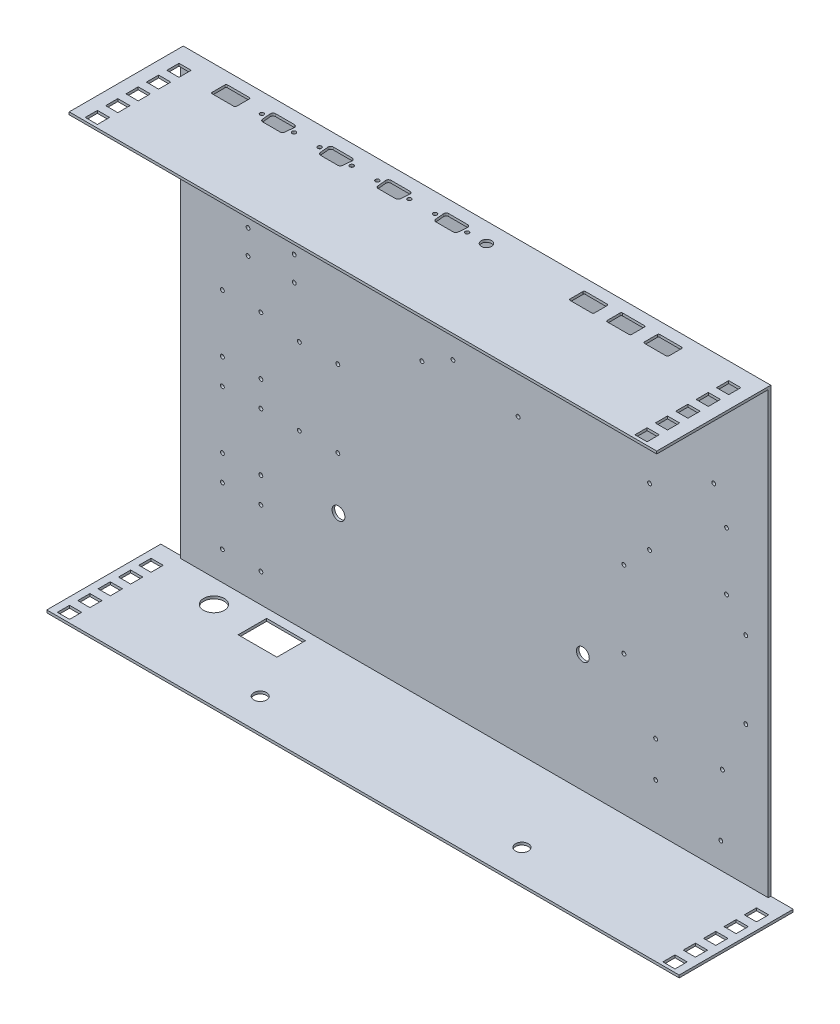
SolidWorks part; units mm, degrees
ref_plane "Front Plane" through (0, 0, 0) normal (0, 0, 1) x (1, 0, 0)
ref_plane "Top Plane" through (0, 0, 0) normal (0, 1, 0) x (1, 0, 0)
ref_plane "Right Plane" through (0, 0, 0) normal (1, 0, 0) x (0, 0, -1)
sketch "Sketch1" plane through (0, 0, 0) normal (0, 0, 1) x (1, 0, 0)
  line L13 (-229, -173.5) -> (229, -173.5)
  line L14 (-229, -173.5) -> (-229, 173.5)
  line L19 (-229, 173.5) -> (229, 173.5)
  line L20 (229, -173.5) -> (229, 173.5)
  line L21 (-229, -173.5) -> (229, 173.5) construction
  line L22 (-229, 173.5) -> (229, -173.5) construction
  point P0 (0, 0)
  dimension "D1" = 458
  dimension "D2" = 347
extrude "Boss-Extrude1" add sketch "Sketch1" along normal blind 2
sketch "Sketch4" plane through (0, -173.5, 0) normal (0, -1, 0) x (1, 0, 0)
  line L0 (-229, 2) -> (-229, 0) construction
  line L1 (-246.5, 0) -> (246.5, 0)
  line L2 (-246.5, 0) -> (-246.5, 88.9)
  line L3 (-246.5, 88.9) -> (246.5, 88.9)
  line L4 (246.5, 0) -> (246.5, 88.9)
  line L5 (229, 2) -> (229, 0) construction
  line L6 (-231.25, 88.9) -> (-231.25, 0) construction
  line L7 (-240.75, 61.02) -> (-231.25, 61.02)
  line L8 (-240.75, 86.4) -> (-231.25, 86.4)
  line L9 (-240.75, 86.4) -> (-240.75, 76.9)
  line L10 (-240.75, 76.9) -> (-231.25, 76.9)
  line L11 (-231.25, 86.4) -> (-231.25, 76.9)
  line L12 (-240.75, 70.52) -> (-240.75, 61.02)
  line L13 (-240.75, 70.52) -> (-231.25, 70.52)
  line L14 (-231.25, 70.52) -> (-231.25, 61.02)
  line L15 (-240.75, 45.14) -> (-231.25, 45.14)
  line L16 (-240.75, 54.64) -> (-240.75, 45.14)
  line L17 (-240.75, 54.64) -> (-231.25, 54.64)
  line L18 (-231.25, 54.64) -> (-231.25, 45.14)
  line L19 (-240.75, 29.26) -> (-231.25, 29.26)
  line L20 (-240.75, 38.76) -> (-240.75, 29.26)
  line L21 (-240.75, 38.76) -> (-231.25, 38.76)
  line L22 (-231.25, 38.76) -> (-231.25, 29.26)
  line L23 (-240.75, 13.38) -> (-231.25, 13.38)
  line L24 (-240.75, 22.88) -> (-240.75, 13.38)
  line L25 (-240.75, 22.88) -> (-231.25, 22.88)
  line L26 (-231.25, 22.88) -> (-231.25, 13.38)
  line L27 (0, 0) -> (0, 101.053) construction
  line L28 (231.25, 22.88) -> (231.25, 13.38)
  line L29 (240.75, 13.38) -> (231.25, 13.38)
  line L30 (240.75, 22.88) -> (240.75, 13.38)
  line L31 (240.75, 22.88) -> (231.25, 22.88)
  line L32 (231.25, 38.76) -> (231.25, 29.26)
  line L33 (240.75, 29.26) -> (231.25, 29.26)
  line L34 (240.75, 38.76) -> (240.75, 29.26)
  line L35 (240.75, 38.76) -> (231.25, 38.76)
  line L36 (240.75, 54.64) -> (240.75, 45.14)
  line L37 (231.25, 54.64) -> (231.25, 45.14)
  line L38 (240.75, 45.14) -> (231.25, 45.14)
  line L39 (240.75, 54.64) -> (231.25, 54.64)
  line L40 (231.25, 70.52) -> (231.25, 61.02)
  line L41 (240.75, 61.02) -> (231.25, 61.02)
  line L42 (240.75, 70.52) -> (231.25, 70.52)
  line L43 (240.75, 70.52) -> (240.75, 61.02)
  line L44 (231.25, 86.4) -> (231.25, 76.9)
  line L45 (240.75, 86.4) -> (231.25, 86.4)
  line L46 (240.75, 86.4) -> (240.75, 76.9)
  line L47 (240.75, 76.9) -> (231.25, 76.9)
  dimension "D1" = 17.5
  dimension "D2" = 17.5
  dimension "D3" = 88.9
  dimension "D4" = 2.25
  dimension "D5" = 9.5
  dimension "D6" = 2.5
  dimension "D7" = 9.5
  dimension "D9" = 15.88
  dimension "D8" = 5
extrude "Boss-Extrude4" add sketch "Sketch4" against normal blind 2
ref_plane "Plane1" through (0, 0, 0) normal (0, 1, 0) x (1, 0, 0)
mirror "Mirror1" about plane through (0, 0, 0) normal (0, 1, 0) of "Boss-Extrude4"
sketch "Sketch5" plane through (0, 173.5, 0) normal (0, 1, 0) x (1, 0, 0)
  line L0 (-229, 0) -> (-229, -88.9) construction
  line L1 (246.5, 0) -> (-246.5, 0) construction
  line L2 (246.5, -88.9) -> (-246.5, -88.9) construction
  line L3 (240.75, -76.9) -> (240.75, -86.4) construction
  line L4 (231.25, -86.4) -> (231.25, -76.9) construction
  line L5 (231.25, -76.9) -> (240.75, -76.9) construction
  line L6 (240.75, -70.52) -> (231.25, -70.52) construction
  line L7 (0, -1.1) -> (0, 1.1) construction
  line L8 (-231.25, -38.76) -> (-240.75, -38.76) construction
  line L9 (-231.25, -22.88) -> (-240.75, -22.88) construction
  line L11 (-229, 0) -> (-246.5, 0)
  line L12 (-229, 0) -> (-229, -88.9)
  line L13 (-229, -88.9) -> (-246.5, -88.9)
  line L14 (-246.5, 0) -> (-246.5, -88.9)
  line L15 (229, 0) -> (246.5, 0)
  line L16 (246.5, 0) -> (246.5, -88.9)
  line L17 (229, -88.9) -> (246.5, -88.9)
  line L18 (229, 0) -> (229, -88.9)
extrude "Cut-Extrude2" cut sketch "Sketch5" against normal up to next
sketch "Sketch6" plane through (0, 173.5, 0) normal (0, 1, 0) x (1, 0, 0)
  line L0 (-229, -88.9) -> (-229, 0) construction
  line L1 (-219, -13.32) -> (-209.5, -13.32)
  line L2 (-219, -13.32) -> (-219, -22.82)
  line L3 (-219, -22.82) -> (-209.5, -22.82)
  line L4 (-209.5, -13.32) -> (-209.5, -22.82)
  line L6 (-219, -29.22) -> (-219, -38.72)
  line L7 (-219, -29.22) -> (-209.5, -29.22)
  line L8 (-219, -38.72) -> (-209.5, -38.72)
  line L9 (-209.5, -29.22) -> (-209.5, -38.72)
  line L10 (-219, -45.12) -> (-219, -54.62)
  line L11 (-219, -45.12) -> (-209.5, -45.12)
  line L12 (-219, -54.62) -> (-209.5, -54.62)
  line L13 (-209.5, -45.12) -> (-209.5, -54.62)
  line L14 (-219, -61.02) -> (-219, -70.52)
  line L15 (-219, -61.02) -> (-209.5, -61.02)
  line L16 (-219, -70.52) -> (-209.5, -70.52)
  line L17 (-209.5, -61.02) -> (-209.5, -70.52)
  line L18 (-219, -76.92) -> (-219, -86.42)
  line L19 (-219, -76.92) -> (-209.5, -76.92)
  line L20 (-219, -86.42) -> (-209.5, -86.42)
  line L21 (-209.5, -76.92) -> (-209.5, -86.42)
  line L22 (0, -48.895) -> (0, 48.895) construction
  line L23 (219, -45.12) -> (209.5, -45.12)
  line L24 (219, -45.12) -> (219, -54.62)
  line L25 (209.5, -45.12) -> (209.5, -54.62)
  line L26 (219, -54.62) -> (209.5, -54.62)
  line L27 (219, -61.02) -> (209.5, -61.02)
  line L28 (209.5, -61.02) -> (209.5, -70.52)
  line L29 (219, -70.52) -> (209.5, -70.52)
  line L30 (219, -61.02) -> (219, -70.52)
  line L31 (219, -76.92) -> (219, -86.42)
  line L32 (219, -86.42) -> (209.5, -86.42)
  line L33 (209.5, -76.92) -> (209.5, -86.42)
  line L34 (219, -76.92) -> (209.5, -76.92)
  line L35 (219, -13.32) -> (219, -22.82)
  line L36 (219, -13.32) -> (209.5, -13.32)
  line L37 (209.5, -13.32) -> (209.5, -22.82)
  line L38 (219, -22.82) -> (209.5, -22.82)
  line L39 (219, -29.22) -> (219, -38.72)
  line L40 (219, -38.72) -> (209.5, -38.72)
  line L41 (209.5, -29.22) -> (209.5, -38.72)
  line L42 (219, -29.22) -> (209.5, -29.22)
  line L43 (229, -88.9) -> (-229, -88.9) construction
  dimension "D1" = 9.5
  dimension "D2" = 9.5
  dimension "D3" = 10
  dimension "D4" = 2.48
  dimension "D6" = 6.4
  dimension "D5" = 5
extrude "Cut-Extrude3" cut sketch "Sketch6" against normal up to next
sketch "Sketch9" plane through (0, 0, 2) normal (0, 0, 1) x (1, 0, 0)
  line L0 (-91, -171.5) -> (-91, 10.5) construction
  line L1 (246.5, -171.5) -> (-246.5, -171.5) construction
  line L2 (77, -171.5) -> (77, 10.5) construction
  line L3 (-229, -171.5) -> (229, -171.5) construction
  line L4 (-91, 10.5) -> (77, 10.5) construction
  line L5 (-229, 171.5) -> (-229, -171.5) construction
  circle A0 centre (-106, -79.5) radius 5
  circle A3 centre (84.5, -79.5) radius 5
  dimension "D5" = 10
  dimension "D6" = 10
  dimension "D1" = 138
  dimension "D2" = 168
  dimension "D3" = 182
  dimension "D8" = 15
  dimension "D9" = 90
  dimension "D14" = 15
  dimension "D15" = 90
extrude "Cut-Extrude4" cut sketch "Sketch9" against normal up to next
sketch "Sketch11" plane through (0, -173.5, 0) normal (0, -1, 0) x (1, 0, 0)
  line L0 (-90, 0) -> (-90, 85.1375) construction
  line L1 (-246.5, 0) -> (246.5, 0) construction
  line L2 (84, 0) -> (84, 87.0276) construction
  line L10 (-246.5, 88.9) -> (-246.5, 0) construction
  line L11 (-90, 79) -> (84, 79) construction
  circle A0 centre (-105, 64) radius 5
  circle A1 centre (99, 64) radius 5
  dimension "D4" = 10
  dimension "D5" = 10
  dimension "D1" = 174
  dimension "D2" = 156.5
  dimension "D3" = 79
  dimension "D6" = 15
  dimension "D7" = 15
  dimension "D8" = 15
  dimension "D9" = 15
extrude "Cut-Extrude5" cut sketch "Sketch11" against normal up to next
sketch "Sketch12" plane through (0, 0, 2) normal (0, 0, 1) x (1, 0, 0)
  line L0 (-229, -171.5) -> (229, -171.5) construction
  line L1 (-199, -151.5) -> (-164, -151.5)
  line L2 (-199, -151.5) -> (-199, -101.5)
  line L3 (-199, -101.5) -> (-164, -101.5)
  line L4 (-164, -151.5) -> (-164, -101.5)
  line L5 (-199, -151.5) -> (-164, -101.5) construction
  line L6 (-199, -101.5) -> (-164, -151.5) construction
  line L7 (-229, 171.5) -> (-229, -171.5) construction
  line L12 (-199, -86.5) -> (-164, -86.5)
  line L13 (-199, -86.5) -> (-199, -36.5)
  line L18 (-199, -36.5) -> (-164, -36.5)
  line L19 (-164, -86.5) -> (-164, -36.5)
  line L20 (-199, -101.5) -> (-199, 47.085) construction
  line L21 (-199, -86.5) -> (-164, -36.5) construction
  line L22 (-199, -36.5) -> (-164, -86.5) construction
  line L23 (-199, -21.5) -> (-164, -21.5)
  line L24 (-199, -21.5) -> (-199, 28.5)
  line L25 (-199, 28.5) -> (-164, 28.5)
  line L26 (-164, -21.5) -> (-164, 28.5)
  line L27 (-199, -21.5) -> (-164, 28.5) construction
  line L28 (-199, 28.5) -> (-164, -21.5) construction
  line L30 (-139, 23.5) -> (-104, 23.5)
  line L31 (-139, 23.5) -> (-139, -41.5)
  line L32 (-139, -41.5) -> (-104, -41.5)
  line L33 (-104, 23.5) -> (-104, -41.5)
  line L34 (-121.5, -41.5) -> (-121.5, 23.5) construction
  line L35 (-139, -9) -> (-104, -9) construction
  circle A0 centre (-196.5, -149) radius 1.5
  circle A1 centre (-166.5, -149) radius 1.5
  circle A2 centre (-166.5, -104) radius 1.5
  circle A3 centre (-196.5, -104) radius 1.5
  circle A12 centre (-196.5, -84) radius 1.5
  circle A13 centre (-166.5, -84) radius 1.5
  circle A14 centre (-166.5, -39) radius 1.5
  circle A15 centre (-196.5, -39) radius 1.5
  circle A16 centre (-196.5, -19) radius 1.5
  circle A17 centre (-166.5, -19) radius 1.5
  circle A18 centre (-166.5, 26) radius 1.5
  circle A19 centre (-196.5, 26) radius 1.5
  circle A20 centre (-136.5, 21) radius 1.5
  circle A21 centre (-106.5, 21) radius 1.5
  circle A22 centre (-106.5, -39) radius 1.5
  circle A23 centre (-136.5, -39) radius 1.5
  point P4 (-181.5, -126.5)
  point P21 (-181.5, -61.5)
  point P34 (-181.5, 3.5)
  point P43 (-181.5, 28.5)
  point P205 (-121.5, -9)
  dimension "D7" = 3
  dimension "D8" = 3
  dimension "D13" = 3
  dimension "D16" = 3
  dimension "D19" = 2.5
  dimension "D22" = 3
  dimension "D20" = 3
  dimension "D27" = 3
  dimension "D30" = 3
  dimension "D34" = 3
  dimension "D36" = 3
  dimension "D41" = 3
  dimension "D44" = 3
  dimension "D51" = 3
  dimension "D52" = 3
  dimension "D53" = 3
  dimension "D54" = 3
  dimension "D1" = 20
  dimension "D2" = 30
  dimension "D3" = 35
  dimension "D4" = 50
  dimension "D5" = 2.5
  dimension "D6" = 2.5
  dimension "D9" = 2.5
  dimension "D10" = 2.5
  dimension "D11" = 2.5
  dimension "D12" = 2.5
  dimension "D14" = 2.5
  dimension "D15" = 2.5
  dimension "D17" = 35
  dimension "D18" = 50
  dimension "D21" = 2.5
  dimension "D23" = 2.5
  dimension "D24" = 2.5
  dimension "D25" = 2.5
  dimension "D26" = 2.5
  dimension "D28" = 2.5
  dimension "D29" = 2.5
  dimension "D31" = 35
  dimension "D32" = 50
  dimension "D33" = 2.5
  dimension "D35" = 2.5
  dimension "D37" = 2.5
  dimension "D38" = 2.5
  dimension "D39" = 2.5
  dimension "D40" = 2.5
  dimension "D42" = 2.5
  dimension "D43" = 2.5
  dimension "D45" = 15
  dimension "D46" = 15
  dimension "D47" = 35
  dimension "D48" = 65
  dimension "D49" = 25
  dimension "D50" = 5
  dimension "D55" = 2.5
  dimension "D56" = 2.5
  dimension "D57" = 2.5
  dimension "D58" = 2.5
  dimension "D59" = 2.5
  dimension "D60" = 2.5
  dimension "D61" = 2.5
  dimension "D62" = 2.5
extrude "Cut-Extrude6" cut sketch "Sketch12" against normal blind 30 contours A0 | A1 | A12 | A13 | A15 | A14 | A16 | A3 | A2 | A17 | A23 | A22 | A20 | A21 | A18 | A19
sketch "Sketch15" plane through (0, 0, 2) normal (0, 0, 1) x (1, 0, 0)
  line L0 (35.28, 104.261) -> (-47.198, 104.261) construction
  line L1 (-179, 56.5) -> (-138, 56.5)
  line L2 (-179, 56.5) -> (-179, 80.5)
  line L3 (-179, 80.5) -> (-138, 80.5)
  line L4 (-138, 56.5) -> (-138, 80.5)
  line L5 (-158.5, 80.5) -> (-158.5, 56.5) construction
  line L6 (-179, 68.5) -> (-138, 68.5) construction
  line L7 (-64, 116.5) -> (56, 116.5)
  line L8 (-64, 116.5) -> (-64, 43.5)
  line L9 (-64, 43.5) -> (56, 43.5)
  line L10 (56, 116.5) -> (56, 43.5)
  line L11 (-4, 43.5) -> (-4, 116.5) construction
  line L12 (-64, 80) -> (56, 80) construction
  line L13 (94, 136.5) -> (189, 136.5)
  line L14 (94, 136.5) -> (94, 84.5)
  line L15 (94, 84.5) -> (189, 84.5)
  line L16 (189, 136.5) -> (189, 84.5)
  line L17 (141.5, 84.5) -> (141.5, 136.5) construction
  line L18 (94, 110.5) -> (189, 110.5) construction
  line L19 (134, 64.5) -> (199, 64.5)
  line L20 (134, 64.5) -> (134, 14.5)
  line L21 (134, 14.5) -> (199, 14.5)
  line L22 (199, 64.5) -> (199, 14.5)
  line L23 (166.5, 14.5) -> (166.5, 64.5) construction
  line L24 (134, 39.5) -> (199, 39.5) construction
  line L25 (114, -0.5) -> (214, -0.5)
  line L26 (114, -0.5) -> (114, -65.5)
  line L27 (114, -65.5) -> (214, -65.5)
  line L28 (214, -0.5) -> (214, -65.5)
  line L29 (164, -65.5) -> (164, -0.5) construction
  line L30 (114, -33) -> (214, -33) construction
  line L31 (138.725, -90.5) -> (214, -90.5)
  line L32 (138.725, -90.5) -> (138.725, -163.5)
  line L33 (138.725, -163.5) -> (214, -163.5)
  line L34 (214, -90.5) -> (214, -163.5)
  line L35 (176.3625, -163.5) -> (176.3625, -90.5) construction
  line L36 (138.725, -127) -> (214, -127) construction
  line L41 (-229, 171.5) -> (-229, -171.5) construction
  line L42 (229, 171.5) -> (-229, 171.5) construction
  line L43 (229, -171.5) -> (229, 171.5) construction
  line L44 (96.5, 87) -> (186.5, 87)
  line L45 (-176.5, 59) -> (-140.5, 59)
  line L46 (-176.5, 59) -> (-176.5, 78)
  line L47 (-176.5, 78) -> (-140.5, 78)
  line L48 (-140.5, 59) -> (-140.5, 78)
  line L49 (-176.5, 59) -> (-140.5, 78) construction
  line L50 (-176.5, 78) -> (-140.5, 59) construction
  line L51 (96.5, 87) -> (96.5, 134)
  line L52 (96.5, 134) -> (186.5, 134)
  line L53 (186.5, 87) -> (186.5, 134)
  line L54 (96.5, 87) -> (186.5, 134) construction
  line L55 (96.5, 134) -> (186.5, 87) construction
  line L56 (136.5, 17) -> (196.5, 17)
  line L57 (136.5, 17) -> (136.5, 62)
  line L58 (136.5, 62) -> (196.5, 62)
  line L59 (196.5, 17) -> (196.5, 62)
  line L60 (136.5, 17) -> (196.5, 62) construction
  line L61 (136.5, 62) -> (196.5, 17) construction
  line L62 (116.5, -63) -> (211.5, -63)
  line L63 (116.5, -63) -> (116.5, -3)
  line L64 (116.5, -3) -> (211.5, -3)
  line L65 (211.5, -63) -> (211.5, -3)
  line L66 (116.5, -63) -> (211.5, -3) construction
  line L67 (116.5, -3) -> (211.5, -63) construction
  line L68 (-52.35, 53.2) -> (56, 53.2)
  line L69 (-52.35, 53.2) -> (-52.35, 106.8)
  line L70 (-52.35, 106.8) -> (56, 106.8)
  line L71 (56, 53.2) -> (56, 106.8)
  line L72 (1.825, 106.8) -> (1.825, 53.2) construction
  line L73 (-52.35, 80) -> (56, 80) construction
  line L74 (-16.75, 104.261) -> (-16.75, 53.2) construction
  line L75 (141.25, -100.35) -> (141.25, -153.65) construction
  line L76 (138.72, -153.65) -> (214, -153.65)
  line L77 (138.72, -153.65) -> (138.72, -100.35)
  line L78 (138.72, -100.35) -> (214, -100.35)
  line L79 (214, -153.65) -> (214, -100.35)
  line L80 (176.36, -100.35) -> (176.36, -153.65) construction
  line L81 (138.72, -127) -> (214, -127) construction
  circle A0 centre (-176.5, 78) radius 1.4993
  circle A1 centre (-176.5, 59) radius 1.5
  circle A2 centre (-140.5, 59) radius 1.5
  circle A3 centre (-140.5, 78) radius 1.5
  circle A4 centre (116.5, -3) radius 1.5
  circle A5 centre (116.5, -63) radius 1.5
  circle A6 centre (211.5, -63) radius 1.5
  circle A7 centre (211.5, -3) radius 1.5
  circle A8 centre (136.5, 62) radius 1.5
  circle A9 centre (136.5, 17) radius 1.5
  circle A10 centre (196.5, 17) radius 1.5
  circle A11 centre (196.5, 62) radius 1.5
  circle A12 centre (96.5, 134) radius 1.5
  circle A13 centre (96.5, 87) radius 1.5
  circle A14 centre (186.5, 87) radius 1.5
  circle A15 centre (186.5, 134) radius 1.5
  circle A16 centre (35.28, 104.261) radius 1.5
  circle A17 centre (-47.198, 104.261) radius 1.5
  circle A18 centre (-40.945, 55.739) radius 1.5
  circle A19 centre (34.01, 55.739) radius 1.5
  circle A20 centre (-16.75, 96.644) radius 1.5
  circle A21 centre (-16.75, 68.735) radius 1.5
  circle A22 centre (193.28, -102.889) radius 1.5
  circle A23 centre (192.015, -151.411) radius 1.5
  circle A24 centre (141.25, -107.967) radius 1.5
  circle A25 centre (141.25, -135.876) radius 1.5
  point P30 (-158.5, 68.5)
  point P39 (141.5, 110.5)
  point P44 (166.5, 39.5)
  point P49 (164, -33)
  point P124 (176.3625, -127)
  point P152 (-4, 80)
  point P164 (-158.5, 68.5)
  point P194 (164, -33)
  point P246 (141.5, 110.5)
  point P275 (166.5, 39.5)
  point P395 (176.36, -127)
  point P605 (1.825, 80)
  dimension "D27" = 2.9987
  dimension "D28" = 3
  dimension "D29" = 3
  dimension "D30" = 3
  dimension "D33" = 3
  dimension "D34" = 3
  dimension "D35" = 3
  dimension "D36" = 3
  dimension "D39" = 3
  dimension "D40" = 3
  dimension "D41" = 3
  dimension "D42" = 3
  dimension "D45" = 3
  dimension "D46" = 3
  dimension "D47" = 3
  dimension "D48" = 3
  dimension "D52" = 3
  dimension "D57" = 3
  dimension "D58" = 3
  dimension "D59" = 3
  dimension "D66" = 3
  dimension "D67" = 3
  dimension "D71" = 3
  dimension "D72" = 3
  dimension "D78" = 3
  dimension "D79" = 3
  dimension "D1" = 50
  dimension "D2" = 115
  dimension "D3" = 24
  dimension "D4" = 41
  dimension "D5" = 73
  dimension "D6" = 120
  dimension "D7" = 73
  dimension "D8" = 75.275
  dimension "D9" = 52
  dimension "D10" = 95
  dimension "D11" = 50
  dimension "D12" = 65
  dimension "D13" = 65
  dimension "D14" = 100
  dimension "D15" = 55
  dimension "D16" = 165
  dimension "D17" = 35
  dimension "D18" = 40
  dimension "D19" = 20
  dimension "D20" = 30
  dimension "D21" = 15
  dimension "D22" = 15
  dimension "D23" = 15
  dimension "D24" = 25
  dimension "D25" = 2.5
  dimension "D26" = 2.5
  dimension "D31" = 2.5
  dimension "D32" = 2.5
  dimension "D37" = 2.5
  dimension "D38" = 2.5
  dimension "D43" = 2.5
  dimension "D44" = 2.5
  dimension "D49" = 53.6
  dimension "D50" = 108.35
  dimension "D51" = 0
  dimension "D53" = 2.539
  dimension "D54" = 20.72
  dimension "D55" = 82.478
  dimension "D56" = 48.522
  dimension "D60" = 48.522
  dimension "D61" = 21.99
  dimension "D62" = 11.405
  dimension "D63" = 52.03
  dimension "D64" = 7.617
  dimension "D65" = 27.909
  dimension "D68" = 75.28
  dimension "D69" = 53.3
  dimension "D70" = 0
  dimension "D73" = 20.72
  dimension "D74" = 2.539
  dimension "D75" = 21.985
  dimension "D76" = 48.522
  dimension "D77" = 52.03
  dimension "D80" = 27.909
  dimension "D81" = 7.617
extrude "Cut-Extrude7" cut sketch "Sketch15" against normal up to next (2 mm away) contours A2 | A1 | A0 | A3 | A17 | A18 | A21 | A20 | A19 | A16 | A12 | A13 | A14 | A15 | A9 | A8 | A11 | A10 | A4 | A5 | A7 | A6 | A25 | A24 | A22 | A23
sketch "Sketch16" plane through (0, 173.5, 0) normal (0, 1, 0) x (1, 0, 0)
  line L0 (-195.0235, -15) -> (195.2186, -15) construction
  line L2 (-147.3524, -9.7) -> (-132.6476, -9.7)
  line L4 (-140, -28.7384) -> (-140, -16.1884) construction
  line L5 (-146.7298, -20.3) -> (-133.2702, -20.3)
  line L8 (-130.45, -9.7) -> (-130.45, -26.4134) construction
  line L9 (229, 0) -> (-229, 0) construction
  line L10 (-102.3524, -9.7) -> (-87.6476, -9.7)
  line L23 (-149.55, -9.7) -> (-149.55, -23.1825) construction
  line L25 (-130.6564, -11.8878) -> (-131.279, -18.4878)
  line L27 (-149.3436, -11.8878) -> (-148.721, -18.4878)
  line L28 (-149.55, -9.7) -> (-149.55, -9.1639) construction
  line L29 (-85.6564, -11.8878) -> (-86.279, -18.4878)
  line L30 (-101.7298, -20.3) -> (-88.2702, -20.3)
  line L31 (-104.3436, -11.8878) -> (-103.721, -18.4878)
  line L32 (-57.3524, -9.7) -> (-42.6476, -9.7)
  line L33 (-40.6564, -11.8878) -> (-41.279, -18.4878)
  line L34 (-56.7298, -20.3) -> (-43.2702, -20.3)
  line L35 (-59.3436, -11.8878) -> (-58.721, -18.4878)
  line L36 (-12.3524, -9.7) -> (2.3524, -9.7)
  line L37 (4.3436, -11.8878) -> (3.721, -18.4878)
  line L38 (-11.7298, -20.3) -> (1.7298, -20.3)
  line L39 (-14.3436, -11.8878) -> (-13.721, -18.4878)
  line L40 (-185.5023, -21) -> (-168.5023, -21)
  line L41 (-186.5023, -20) -> (-186.5023, -10)
  line L42 (-185.5023, -9) -> (-168.5023, -9)
  line L43 (-167.5023, -20) -> (-167.5023, -10)
  line L44 (-186.5023, -21) -> (-167.5023, -9) construction
  line L45 (-186.5023, -9) -> (-167.5023, -21) construction
  line L46 (122.5023, -21) -> (139.5023, -21)
  line L47 (121.5023, -20) -> (121.5023, -10)
  line L48 (122.5023, -9) -> (139.5023, -9)
  line L49 (140.5023, -20) -> (140.5023, -10)
  line L50 (121.5023, -21) -> (140.5023, -9) construction
  line L51 (121.5023, -9) -> (140.5023, -21) construction
  line L52 (151.5023, -21) -> (168.5023, -21)
  line L53 (150.5023, -20) -> (150.5023, -10)
  line L54 (151.5023, -9) -> (168.5023, -9)
  line L55 (169.5023, -20) -> (169.5023, -10)
  line L56 (150.5023, -21) -> (169.5023, -9) construction
  line L57 (150.5023, -9) -> (169.5023, -21) construction
  line L58 (93.5023, -21) -> (110.5023, -21)
  line L59 (92.5023, -20) -> (92.5023, -10)
  line L60 (93.5023, -9) -> (110.5023, -9)
  line L61 (111.5023, -20) -> (111.5023, -10)
  line L62 (92.5023, -21) -> (111.5023, -9) construction
  line L63 (92.5023, -9) -> (111.5023, -21) construction
  arc A31 (-131.279, -18.4878) -> (-133.2702, -20.3) centre (-133.2702, -18.3) cw
  arc A32 (-146.7298, -20.3) -> (-148.721, -18.4878) centre (-146.7298, -18.3) cw
  arc A33 (-130.6564, -11.8878) -> (-132.6476, -9.7) centre (-132.6476, -11.7) ccw
  arc A34 (-149.3436, -11.8878) -> (-147.3524, -9.7) centre (-147.3524, -11.7) cw
  circle A35 centre (-152.5023, -15.1878) radius 1.5
  circle A36 centre (-127.4977, -15.1878) radius 1.5
  arc A37 (-85.6564, -11.8878) -> (-87.6476, -9.7) centre (-87.6476, -11.7) ccw
  arc A38 (-86.279, -18.4878) -> (-88.2702, -20.3) centre (-88.2702, -18.3) cw
  arc A39 (-101.7298, -20.3) -> (-103.721, -18.4878) centre (-101.7298, -18.3) cw
  arc A40 (-104.3436, -11.8878) -> (-102.3524, -9.7) centre (-102.3524, -11.7) cw
  circle A41 centre (-107.5023, -15.1878) radius 1.5
  circle A42 centre (-82.4977, -15.1878) radius 1.5
  arc A43 (-40.6564, -11.8878) -> (-42.6476, -9.7) centre (-42.6476, -11.7) ccw
  arc A44 (-41.279, -18.4878) -> (-43.2702, -20.3) centre (-43.2702, -18.3) cw
  arc A45 (-56.7298, -20.3) -> (-58.721, -18.4878) centre (-56.7298, -18.3) cw
  arc A46 (-59.3436, -11.8878) -> (-57.3524, -9.7) centre (-57.3524, -11.7) cw
  circle A47 centre (-62.5023, -15.1878) radius 1.5
  circle A48 centre (-37.4977, -15.1878) radius 1.5
  arc A49 (4.3436, -11.8878) -> (2.3524, -9.7) centre (2.3524, -11.7) ccw
  arc A50 (3.721, -18.4878) -> (1.7298, -20.3) centre (1.7298, -18.3) cw
  arc A51 (-11.7298, -20.3) -> (-13.721, -18.4878) centre (-11.7298, -18.3) cw
  arc A52 (-14.3436, -11.8878) -> (-12.3524, -9.7) centre (-12.3524, -11.7) cw
  circle A53 centre (-17.5023, -15.1878) radius 1.5
  circle A54 centre (7.5023, -15.1878) radius 1.5
  circle A55 centre (22.5023, -15.1878) radius 4
  arc A56 (-185.5023, -21) -> (-186.5023, -20) centre (-185.5023, -20) cw
  arc A57 (-168.5023, -21) -> (-167.5023, -20) centre (-168.5023, -20) ccw
  arc A58 (-168.5023, -9) -> (-167.5023, -10) centre (-168.5023, -10) cw
  arc A59 (-186.5023, -10) -> (-185.5023, -9) centre (-185.5023, -10) cw
  arc A60 (122.5023, -21) -> (121.5023, -20) centre (122.5023, -20) cw
  arc A61 (139.5023, -21) -> (140.5023, -20) centre (139.5023, -20) ccw
  arc A62 (139.5023, -9) -> (140.5023, -10) centre (139.5023, -10) cw
  arc A63 (121.5023, -10) -> (122.5023, -9) centre (122.5023, -10) cw
  arc A64 (151.5023, -21) -> (150.5023, -20) centre (151.5023, -20) cw
  arc A65 (168.5023, -21) -> (169.5023, -20) centre (168.5023, -20) ccw
  arc A66 (168.5023, -9) -> (169.5023, -10) centre (168.5023, -10) cw
  arc A67 (150.5023, -10) -> (151.5023, -9) centre (151.5023, -10) cw
  arc A68 (93.5023, -21) -> (92.5023, -20) centre (93.5023, -20) cw
  arc A69 (110.5023, -21) -> (111.5023, -20) centre (110.5023, -20) ccw
  arc A70 (110.5023, -9) -> (111.5023, -10) centre (110.5023, -10) cw
  arc A71 (92.5023, -10) -> (93.5023, -9) centre (93.5023, -10) cw
  point P6 (-140, -9.7)
  point P10 (-149.0323, -15.1878)
  point P12 (-130.9677, -15.1878)
  point P30 (-177.0023, -15)
  point P83 (8.0147, -15.1377)
  point P99 (-195.0235, -15.1878)
  point P100 (-47.5633, -15.1878)
  point P101 (132.5559, -15.1878)
  point P102 (195.2186, -15.1878)
  point P103 (131.0023, -15)
  point P120 (160.0023, -15)
  point P137 (102.0023, -15)
  dimension "D5" = 2
  dimension "D8" = 7.3524
  dimension "D9" = 3
  dimension "D13" = 0.1878
  dimension "D16" = 8
  dimension "D22" = 19
  dimension "D10" = 3
  dimension "D20" = 1
  dimension "D24" = 1
  dimension "D27" = 1
  dimension "D30" = 1
  dimension "D1" = 5.3
  dimension "D2" = 19.1
  dimension "D3" = 5.3
  dimension "D4" = 5.389
  dimension "D6" = 15
  dimension "D7" = 140
  dimension "D11" = 3.47
  dimension "D12" = 3.47
  dimension "D15" = 19.9954
  dimension "D17" = 15
  dimension "D18" = 19
  dimension "D19" = 12
  dimension "D21" = 15
  dimension "D14" = 0.1878
  dimension "D23" = 12
  dimension "D25" = 19
  dimension "D26" = 12
  dimension "D28" = 19
  dimension "D29" = 12
  dimension "D31" = 10
  dimension "D32" = 10
  dimension "D33" = 70
extrude "Cut-Extrude9" cut sketch "Sketch16" against normal up to next
sketch "Sketch17" plane through (0, -173.5, 0) normal (0, -1, 0) x (1, 0, 0)
  line L0 (-246.5, 0) -> (246.5, 0) construction
  line L1 (-155.1, 31.1) -> (-124.9, 31.1)
  line L2 (-155.1, 31.1) -> (-155.1, 8.9)
  line L3 (-155.1, 8.9) -> (-124.9, 8.9)
  line L4 (-124.9, 31.1) -> (-124.9, 8.9)
  line L5 (-155.1, 31.1) -> (-124.9, 8.9) construction
  line L6 (-155.1, 8.9) -> (-124.9, 31.1) construction
  circle A0 centre (-185.1, 20) radius 8.05
  point P0 (-140, 20)
  point P12 (-150, 20)
  dimension "D5" = 16.1
  dimension "D1" = 22.2
  dimension "D2" = 30.2
  dimension "D3" = 140
  dimension "D4" = 20
  dimension "D6" = 30
extrude "Cut-Extrude10" cut sketch "Sketch17" against normal up to next
